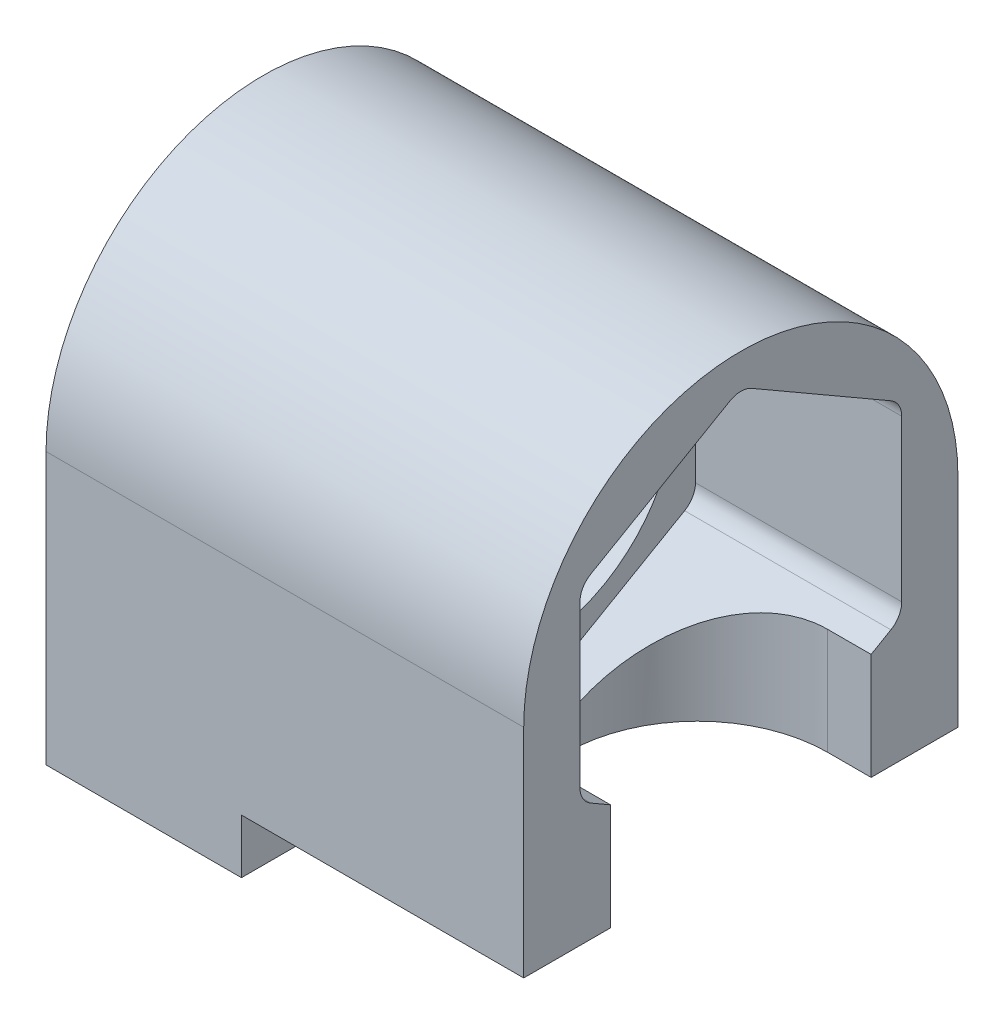
SolidWorks part; units mm, degrees
material "ABS"
ref_plane "Ebene vorne" through (0, 0, 0) normal (0, 0, 1) x (1, 0, 0)
ref_plane "Ebene oben" through (0, 0, 0) normal (0, 1, 0) x (1, 0, 0)
ref_plane "Ebene rechts" through (0, 0, 0) normal (1, 0, 0) x (0, 0, -1)
sketch "Skizze1" plane through (0, 0, 0) normal (1, 0, 0) x (0, 0, -1)
  line L0 (-10, 0) -> (-10, -12.5)
  line L1 (-10, -12.5) -> (10, -12.5)
  line L2 (10, -12.5) -> (10, 0)
  circle A0 centre (0, 0) radius 6.5
  arc A1 (-10, 0) -> (10, 0) centre (0, 0) cw
  dimension "D1" = 13
  dimension "D2" = 20
  dimension "D3" = 12.5
extrude "Aufsatz-Linear austragen1" add sketch "Skizze1" along normal blind 22
sketch "Skizze2" plane through (22, 0, 0) normal (1, 0, 0) x (0, 0, -1)
  line L1 (7.4106, -3.7012) -> (7.4106, 3.7012)
  line L2 (6.9106, 4.5672) -> (0.5, 8.2684)
  line L3 (-0.5, 8.2684) -> (-6.9106, 4.5672)
  line L4 (-7.4106, 3.7012) -> (-7.4106, -3.7012)
  line L5 (-6.9106, -4.5672) -> (-0.5, -8.2684)
  line L6 (0.5, -8.2684) -> (6.9106, -4.5672)
  circle A1 centre (0, 0) radius 7.4106 construction
  arc A2 (-7.4106, -3.7012) -> (-6.9106, -4.5672) centre (-6.4106, -3.7012) ccw
  arc A3 (-0.5, -8.2684) -> (0.5, -8.2684) centre (0, -7.4024) ccw
  arc A4 (7.4106, -3.7012) -> (6.9106, -4.5672) centre (6.4106, -3.7012) cw
  arc A5 (7.4106, 3.7012) -> (6.9106, 4.5672) centre (6.4106, 3.7012) ccw
  arc A6 (0.5, 8.2684) -> (-0.5, 8.2684) centre (0, 7.4024) ccw
  arc A7 (-6.9106, 4.5672) -> (-7.4106, 3.7012) centre (-6.4106, 3.7012) ccw
  dimension "D1" = 14.8213
  dimension "D2" = 1
extrude "Schnitt-Linear austragen1" cut sketch "Skizze2" against normal blind 9.5
sketch "Skizze3" plane through (0, -12.5, 0) normal (0, -1, 0) x (1, 0, 0)
  line L0 (0, 0) -> (10.0445, 0) construction
  line L1 (22, 10) -> (22, -10) construction
  circle A0 centre (5, 5) radius 2.75
  circle A1 centre (5, -5) radius 2.75
  dimension "D1" = 10
  dimension "D3" = 5.5
  dimension "D2" = 17
extrude "Schnitt-Linear austragen2" cut sketch "Skizze3" against normal blind 6
sketch "Skizze4" plane through (0, -12.5, 0) normal (0, -1, 0) x (1, 0, 0)
  line L0 (20, 6) -> (22, 6)
  line L1 (22, 10) -> (22, -10) construction
  line L2 (22, 6) -> (22, -6)
  line L3 (22, -6) -> (20, -6)
  arc A0 (20, 6) -> (20, -6) centre (20, 0) ccw
  dimension "D1" = 12
  dimension "D2" = 2
extrude "Schnitt-Linear austragen3" cut sketch "Skizze4" against normal up to next
sketch "Skizze5" plane through (0, -12.5, 0) normal (0, -1, 0) x (1, 0, 0)
  line L0 (22, 10) -> (0, 10) construction
  line L1 (9, 10) -> (22, 10)
  line L2 (9, 10) -> (9, -10)
  line L3 (9, -10) -> (22, -10)
  line L4 (22, 10) -> (22, -10)
  dimension "D2" = 13
extrude "Schnitt-Linear austragen4" cut sketch "Skizze5" against normal blind 2.5
